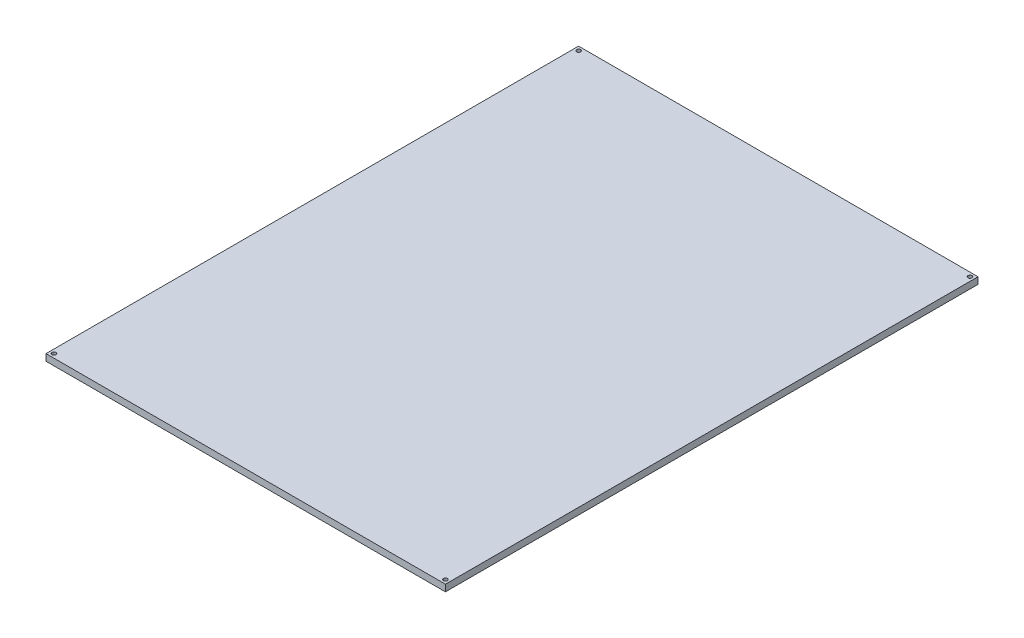
SolidWorks part; units mm, degrees
ref_plane "Спереди" through (0, 0, 0) normal (0, 0, 1) x (1, 0, 0)
ref_plane "Сверху" through (0, 0, 0) normal (0, 1, 0) x (1, 0, 0)
ref_plane "Справа" through (0, 0, 0) normal (1, 0, 0) x (0, 0, -1)
sketch "Эскиз1" plane through (0, 0, 0) normal (0, 1, 0) x (1, 0, 0)
  line L1 (-150, -200) -> (150, -200)
  line L2 (-150, -200) -> (-150, 200)
  line L3 (-150, 200) -> (150, 200)
  line L4 (150, -200) -> (150, 200)
  dimension "D1" = 300
  dimension "D2" = 400
  dimension "D3" = 200
  dimension "D4" = 150
extrude "Бобышка-Вытянуть1" add sketch "Эскиз1" along normal blind 5
sketch "Эскиз2" plane through (0, 5, 0) normal (0, 1, 0) x (1, 0, 0)
  line L0 (150, 200) -> (-150, 200) construction
  line L1 (-150, 200) -> (-150, -200) construction
  line L2 (-150, -200) -> (150, -200) construction
  line L3 (150, -200) -> (150, 200) construction
  circle A0 centre (-147, 197) radius 1.5
  circle A1 centre (147, 197) radius 1.5
  circle A2 centre (147, -197) radius 1.5
  circle A3 centre (-147, -197) radius 1.5
  dimension "D1" = 3
  dimension "D2" = 3
  dimension "D3" = 3
  dimension "D6" = 3
  dimension "D7" = 3
  dimension "D8" = 3
  dimension "D9" = 3
  dimension "D4" = 2
  dimension "D5" = 2
extrude "Вырез-Вытянуть1" cut sketch "Эскиз2" against normal blind 5
sketch "Эскиз4" plane through (0, 5, 0) normal (0, 1, 0) x (1, 0, 0)
  line L0 (148.5, -197) -> (145.5, -197) construction
  circle A0 centre (147, -197) radius 1.5 construction
  point P5 (147, -197)
  point P6 (-147, -197)
  point P7 (-147, 197)
  point P9 (147, 197)
